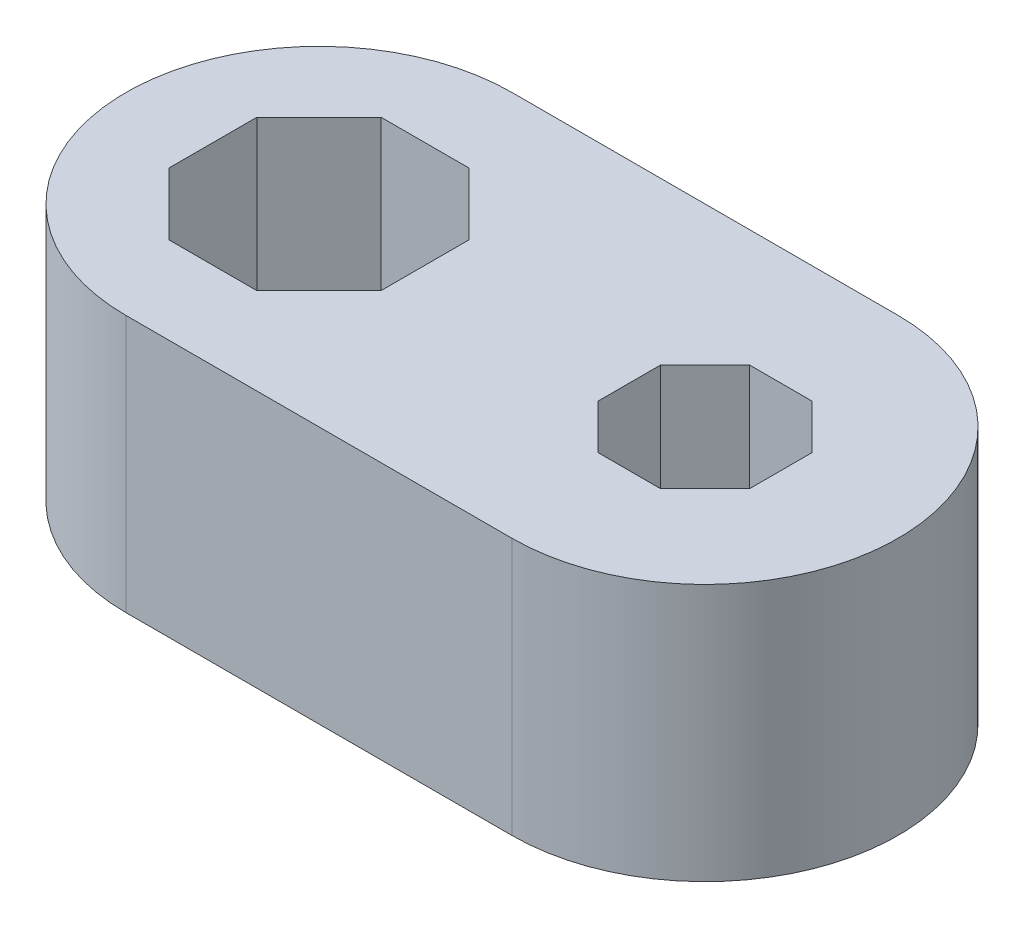
SolidWorks part; units mm, degrees
ref_plane "Front Plane" through (0, 0, 0) normal (0, 0, 1) x (1, 0, 0)
ref_plane "Top Plane" through (0, 0, 0) normal (0, 1, 0) x (1, 0, 0)
ref_plane "Right Plane" through (0, 0, 0) normal (1, 0, 0) x (0, 0, -1)
sketch "Sketch1" plane through (0, 0, 0) normal (0, 1, 0) x (1, 0, 0)
  line L0 (0, -3.8574) -> (0, 3.8574) construction
  line L1 (-4.6338, 3.2983) -> (-7.3662, 3.2983)
  line L2 (-7.3662, 3.2983) -> (-9.2983, 1.3662)
  line L3 (-9.2983, 1.3662) -> (-9.2983, -1.3662)
  line L4 (-9.2983, -1.3662) -> (-7.3662, -3.2983)
  line L5 (-7.3662, -3.2983) -> (-4.6338, -3.2983)
  line L6 (-4.6338, -3.2983) -> (-2.7017, -1.3662)
  line L7 (-2.7017, -1.3662) -> (-2.7017, 1.3662)
  line L8 (-2.7017, 1.3662) -> (-4.6338, 3.2983)
  line L9 (8.3559, 0.9758) -> (6.9758, 2.3559)
  line L10 (6.9758, 2.3559) -> (5.0242, 2.3559)
  line L11 (5.0242, 2.3559) -> (3.6441, 0.9758)
  line L12 (3.6441, 0.9758) -> (3.6441, -0.9758)
  line L13 (3.6441, -0.9758) -> (5.0242, -2.3559)
  line L14 (5.0242, -2.3559) -> (6.9758, -2.3559)
  line L15 (6.9758, -2.3559) -> (8.3559, -0.9758)
  line L16 (8.3559, -0.9758) -> (8.3559, 0.9758)
  line L17 (-6, 6) -> (6, 6)
  line L18 (-6, -6) -> (6, -6)
  circle A0 centre (-6, 0) radius 3.2983 construction
  arc A1 (-6, 6) -> (-6, -6) centre (-6, 0) ccw
  circle A2 centre (6, 0) radius 2.3559 construction
  arc A3 (6, 6) -> (6, -6) centre (6, 0) cw
  point P26 (0, 0)
  dimension "D2" = 12
  dimension "D1" = 2.7324
  dimension "D3" = 1.9517
extrude "Boss-Extrude1" add sketch "Sketch1" along normal blind 8
